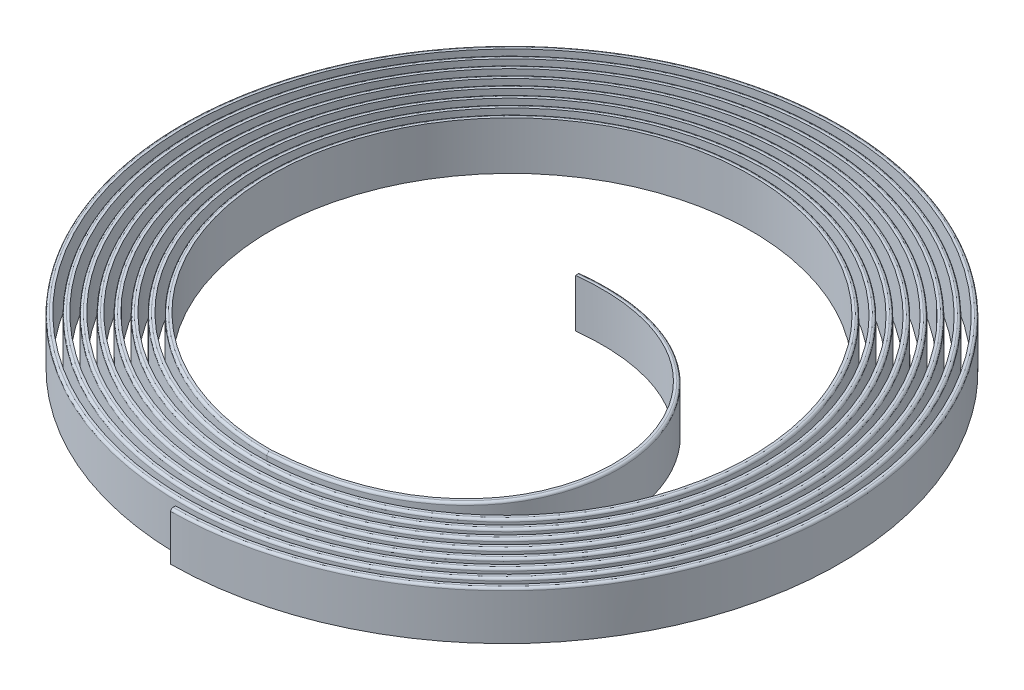
SolidWorks part; units mm, degrees
ref_plane "Front Plane" through (0, 0, 0) normal (0, 0, 1) x (1, 0, 0)
ref_plane "Top Plane" through (0, 0, 0) normal (0, 1, 0) x (1, 0, 0)
ref_plane "Right Plane" through (0, 0, 0) normal (1, 0, 0) x (0, 0, -1)
sketch "Sketch1" plane through (0, 0, 0) normal (0, 1, 0) x (1, 0, 0)
  circle A0 centre (0, 0) radius 7
  dimension "D1" = 14
curve "Helix/Spiral1"
sketch "Sketch2" plane through (0, 0, 0) normal (0, 1, 0) x (1, 0, 0)
  circle A0 centre (0, 0) radius 1.5 construction
  spline S0 degree 3 poles (0, -5) (5.549, -4.6557) (4.8159, 2.0307) (0, 1.5) knots 0 0 0 0 1 1 1 1
  dimension "D1" = 3
curve "CompCurve1"
sketch "Sketch3" plane through (0, 0, 0) normal (1, 0, 0) x (0, 0, -1)
  line L0 (-7, 0) -> (-7, 1)
  line L1 (-7, 0) -> (-6.9, 0)
  line L2 (-6.9, 0) -> (-6.9, 1)
  line L3 (-6.9, 1) -> (-7, 1)
  dimension "D1" = 1
  dimension "D2" = 0.1
sweep "Sweep1" add profiles "Sketch3" path "CompCurve1"
fillet "Fillet1" radius 0.05 2 edges
